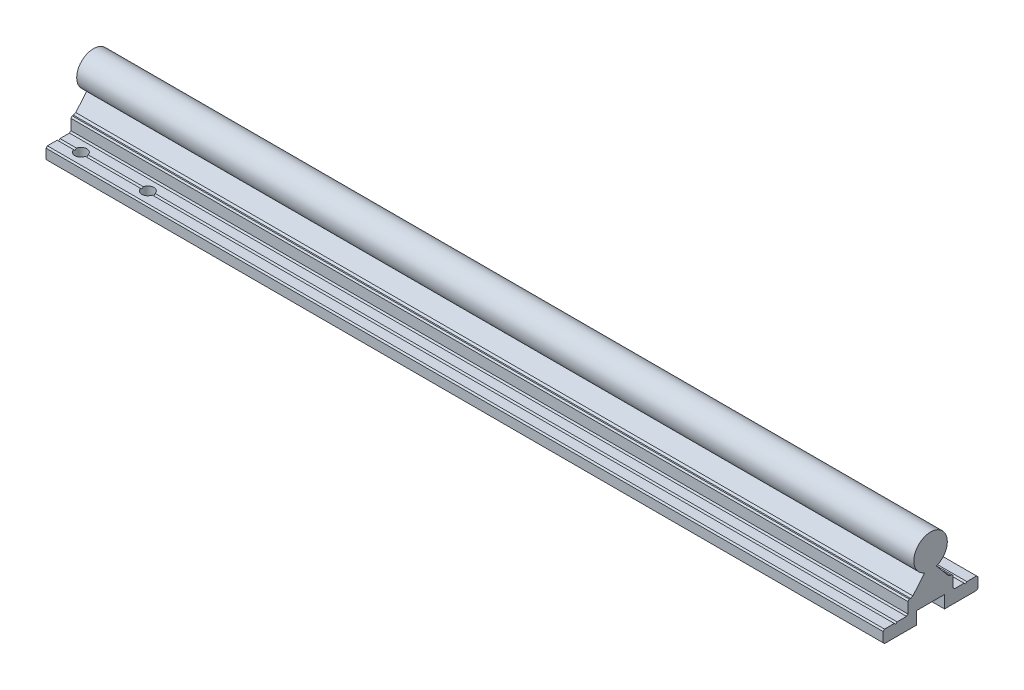
SolidWorks part; units mm, degrees
ref_plane "前视基准面" through (0, 0, 0) normal (0, 0, 1) x (1, 0, 0)
ref_plane "上视基准面" through (0, 0, 0) normal (0, 1, 0) x (1, 0, 0)
ref_plane "右视基准面" through (0, 0, 0) normal (1, 0, 0) x (0, 0, -1)
sketch "Sketch1" plane through (0, 0, 0) normal (1, 0, 0) x (0, 0, -1)
  line L0 (-2.1041, 2.6541) -> (-6.3397, -2.3936)
  line L2 (6.3397, -2.3936) -> (2.1041, 2.6541)
  line L3 (0, 5.1617) -> (0, -12.1269) construction
  line L5 (8.1004, -7.1269) -> (8.1004, -3.2767)
  line L6 (7.6004, -2.7767) -> (7.1611, -2.7767)
  line L7 (-8.1004, -7.1269) -> (-8.1004, -3.2767)
  line L8 (8.1004, -7.6269) -> (-8.1004, -2.7767) construction
  line L9 (8.1004, -2.7767) -> (-8.1004, -7.6269) construction
  line L10 (16.5, -12.1269) -> (5, -12.1269)
  line L11 (17, -11.6269) -> (17, -8.1269)
  line L12 (16.5, -7.6269) -> (13, -7.6269)
  line L13 (-17, -11.6269) -> (-17, -8.1269)
  line L14 (17, -12.1269) -> (-17, -7.6269) construction
  line L15 (17, -7.6269) -> (-17, -12.1269) construction
  line L16 (-6.9391, 0.0035) -> (0, 8.2731) construction
  line L17 (0, 8.2731) -> (6.8403, 0.1211) construction
  line L18 (-3.8567, 3.6769) -> (3.8567, 3.6769) construction
  line L19 (-7.1611, -2.7767) -> (-7.6004, -2.7767)
  line L20 (-8.6004, -7.6269) -> (-12, -7.6269)
  line L21 (-16.5, -7.6269) -> (-17, -8.1269)
  line L22 (-16.5, -12.1269) -> (-17, -11.6269)
  line L23 (17, -8.1269) -> (16.5, -7.6269)
  line L24 (17, -11.6269) -> (16.5, -12.1269)
  line L25 (8.6004, -7.6269) -> (8.1004, -7.1269)
  line L26 (-8.1004, -7.1269) -> (-8.6004, -7.6269)
  line L27 (8.1004, -3.2767) -> (7.6004, -2.7767)
  line L28 (-7.6004, -2.7767) -> (-8.1004, -3.2767)
  line L29 (-6.3397, -2.3936) -> (-7.1611, -2.7767)
  line L30 (7.1611, -2.7767) -> (6.3397, -2.3936)
  line L31 (-12.5, -7.5329) -> (-12.5, -12.1269) construction
  line L32 (12.5, -7.5329) -> (12.5, -12.1269) construction
  line L33 (-13, -7.6269) -> (-12.5, -8.1269)
  line L34 (-12.5, -8.1269) -> (-12, -7.6269)
  line L35 (-13, -7.6269) -> (-16.5, -7.6269)
  line L36 (12.5, -8.1269) -> (12, -7.6269)
  line L37 (13, -7.6269) -> (12.5, -8.1269)
  line L38 (12, -7.6269) -> (8.6004, -7.6269)
  line L39 (-5, -12.1269) -> (-16.5, -12.1269)
  line L41 (5, -12.1269) -> (5, -7.6269)
  line L42 (5, -7.6269) -> (-5, -7.6269)
  line L43 (-5, -12.1269) -> (-5, -7.6269)
  arc A1 (2.1041, 2.6541) -> (-2.1041, 2.6541) centre (0, 8.2731) ccw
  point P2 (6.6611, -2.7767)
  point P3 (-6.6611, -2.7767)
  point P4 (0, -5.2018)
  point P9 (0, -9.8769)
  dimension "D2" = 12
  dimension "D1" = 80
  dimension "D3" = 4.5
  dimension "D4" = 34
  dimension "D5" = 20.4
  dimension "D6" = 2
  dimension "D7" = 2
  dimension "D8" = 7.7135
  dimension "D9" = 45
  dimension "D10" = 0.5
  dimension "D21" = 25
  dimension "D22" = 5
  dimension "D23" = 5
extrude "Extrude1" add sketch "Sketch1" along normal blind 300
sketch "Sketch2" plane through (0, -12.1269, 0) normal (0, -1, 0) x (1, 0, 0)
  circle A0 centre (32, -12.5) radius 2.15 construction
  circle A1 centre (8, -12.5) radius 2.15 construction
  circle A2 centre (32, 12.5) radius 2.15 construction
  circle A3 centre (8, 12.5) radius 2.15 construction
  circle A4 centre (32, -12.5) radius 2.15
  circle A5 centre (8, -12.5) radius 2.15
  circle A6 centre (32, 12.5) radius 2.15
  circle A7 centre (8, 12.5) radius 2.15
extrude "Cut-Extrude1" cut sketch "Sketch2" against normal blind 10
